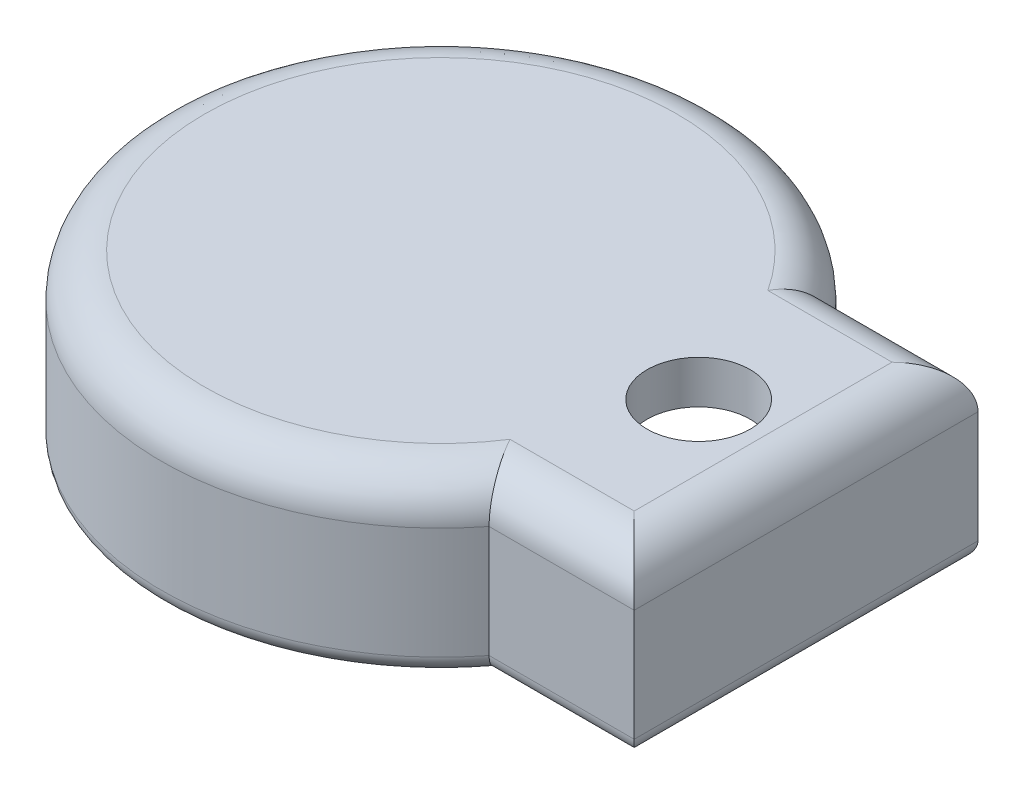
SolidWorks part; units mm, degrees
ref_plane "Plan de face" through (0, 0, 0) normal (0, 0, 1) x (1, 0, 0)
ref_plane "Plan de dessus" through (0, 0, 0) normal (0, 1, 0) x (1, 0, 0)
ref_plane "Plan de droite" through (0, 0, 0) normal (1, 0, 0) x (0, 0, -1)
sketch "Esquisse1" plane through (0, 0, 0) normal (0, 1, 0) x (1, 0, 0)
  line L0 (25.6174, 20) -> (42.5, 20)
  line L1 (17.5, -15) -> (37.5, -15)
  line L2 (17.5, -15) -> (17.5, 15)
  line L3 (17.5, 15) -> (37.5, 15)
  line L4 (37.5, -15) -> (37.5, 15)
  line L5 (17.5, -15) -> (37.5, 15) construction
  line L6 (17.5, 15) -> (37.5, -15) construction
  line L7 (42.5, -20) -> (42.5, 20)
  line L8 (25.6174, -20) -> (42.5, -20)
  line L9 (17.5, 20) -> (42.5, 20) construction
  line L10 (17.5, -20) -> (42.5, -20) construction
  circle A0 centre (0, 0) radius 27.5
  circle A2 centre (0, 0) radius 32.5
  point P3 (27.5, 0)
  dimension "D1" = 55
  dimension "D2" = 30
  dimension "D3" = 20
  dimension "D4" = 5
  dimension "D5" = 5
extrude "Boss.-Extru.1" add sketch "Esquisse1" along normal blind 15 contours A2 L1 A0 L3 | A2 L8 L7 L0 L3 L4 L1
sketch "Esquisse2" plane through (0, 15, 0) normal (0, 1, 0) x (1, 0, 0)
  line L3 (42.5, 20) -> (25.6174, 20)
  line L4 (25.6174, -20) -> (42.5, -20)
  line L5 (42.5, -20) -> (42.5, 20)
  line L6 (42.5, 20) -> (25.6174, 20)
  line L7 (25.6174, -20) -> (42.5, -20)
  line L8 (42.5, -20) -> (42.5, 20)
  circle A0 centre (30, 0) radius 6
  arc A1 (25.6174, 20) -> (25.6174, -20) centre (0, 0) ccw
  arc A2 (25.6174, 20) -> (25.6174, -20) centre (0, 0) ccw
  point P7 (42.5, 0)
  dimension "D2" = 12.5
  dimension "D3" = 12
  dimension "D1" = 0
extrude "Boss.-Extru.2" add sketch "Esquisse2" along normal blind 5
fillet "Congé1" radius 5 4 edges at (34.0587, 20, 20) (42.5, 20, 0) (34.0587, 20, -20) (-32.5, 20, 0)
fillet "Congé2" radius 2 8 edges at (37.5, 0, 0) (30.2744, 0, 15) (-27.5, 0, 0) (30.2744, 0, -15) (-32.5, 0, 0) (34.0587, 0, 20) (42.5, 0, 0) (34.0587, 0, -20)
